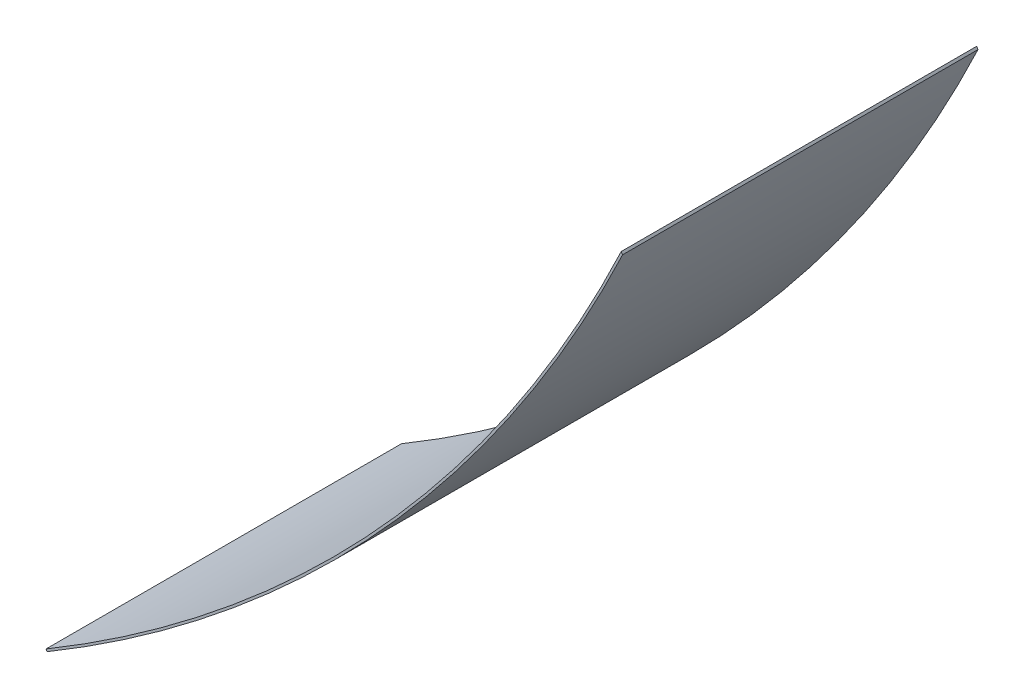
SolidWorks part; units mm, degrees
material "PC High Viscosity"
ref_plane "Front Plane" through (0, 0, 0) normal (0, 0, 1) x (1, 0, 0)
ref_plane "Top Plane" through (0, 0, 0) normal (0, 1, 0) x (1, 0, 0)
ref_plane "Right Plane" through (0, 0, 0) normal (1, 0, 0) x (0, 0, -1)
sketch "Sketch1" plane through (0, 0, 0) normal (0, 0, 1) x (1, 0, 0)
  line L2 (2736.8131, 2975.2532) -> (2742.9025, 2964.751) construction
  line L4 (2736.8131, 2975.2532) -> (2743.0332, 2965.0264)
  line L5 (65.4811, 26.8245) -> (60.3764, 35.4234)
  arc A3 (60.3764, 35.4234) -> (2736.8131, 2975.2532) centre (-3412.3492, 5885.2474) ccw
  arc A4 (65.4811, 26.8245) -> (2743.0332, 2965.0264) centre (-3412.3492, 5885.2474) ccw
  arc A5 (65.4811, 26.8245) -> (2745.8521, 2970.9757) centre (-3412.3492, 5885.2474) ccw construction
  dimension "D1" = 10
extrude "Boss-Extrude1" add sketch "Sketch1" along normal up to surface (1653.7276 mm away)
